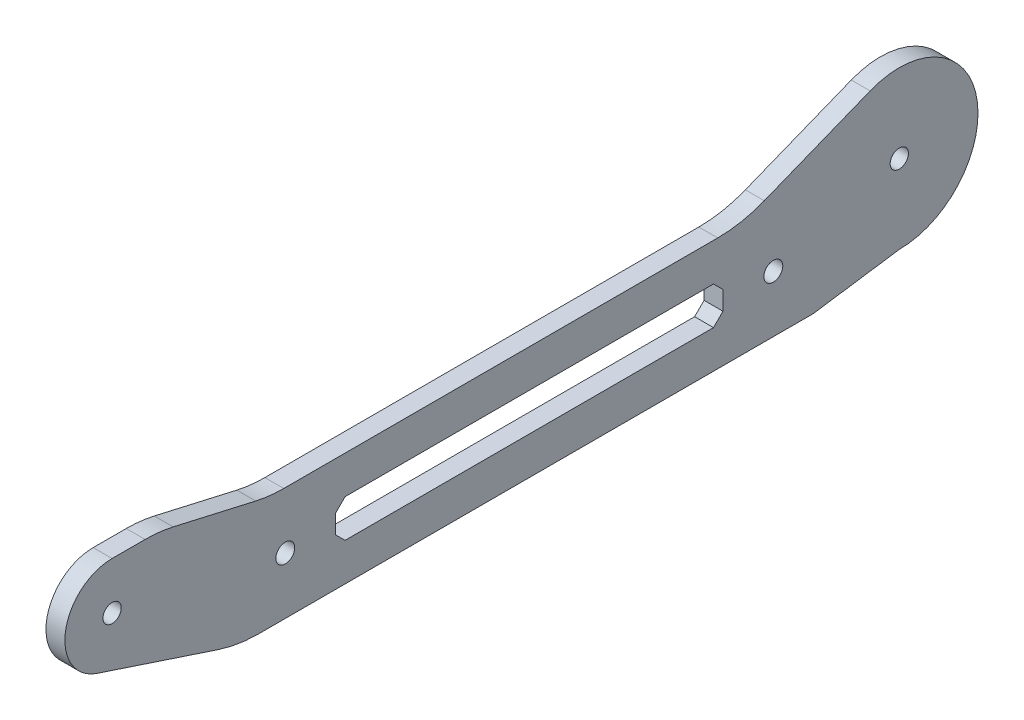
SolidWorks part; units mm, degrees
ref_plane "Front Plane" through (0, 0, 0) normal (0, 0, 1) x (1, 0, 0)
ref_plane "Top Plane" through (0, 0, 0) normal (0, 1, 0) x (1, 0, 0)
ref_plane "Right Plane" through (0, 0, 0) normal (1, 0, 0) x (0, 0, -1)
sketch "Sketch1" plane through (0, 0, 0) normal (1, 0, 0) x (0, 0, -1)
  line L0 (0, 0) -> (-125, 0) construction
  line L1 (-105, -14.5) -> (-13.675, -14.5)
  line L2 (-105, -14.5) -> (-127.351, -7.122)
  line L3 (-125, 7.5) -> (-117.5, 7.5)
  line L4 (-117.5, 7.5) -> (-100, 3.5)
  line L5 (-100, 3.5) -> (-25, 3.5)
  line L6 (-25, 3.5) -> (-4.6241, 11.6132)
  line L7 (-89.5, -4) -> (-88, -2.5)
  line L8 (-60, -5.5) -> (-97.5, -5.5) construction
  line L9 (-60, -5.5) -> (-20, -5.5) construction
  line L10 (-88, -2.5) -> (-29.5, -2.5)
  line L11 (-89.5, -4) -> (-89.5, -7)
  line L12 (-88, -8.5) -> (-29.5, -8.5)
  line L13 (-13.675, -14.5) -> (0, -12.5)
  line L14 (-28, -4) -> (-28, -7)
  line L15 (-89.5, -7) -> (-88, -8.5)
  line L16 (-29.5, -2.5) -> (-28, -4)
  line L17 (-29.5, -8.5) -> (-28, -7)
  line L19 (0, 0) -> (7.675, 0) construction
  line L20 (7.675, 0) -> (10.675, 0) construction
  line L21 (10.675, 0) -> (13.675, 0) construction
  circle A0 centre (3.8375, -6.6467) radius 1.075 construction
  circle A1 centre (5.3375, -9.2448) radius 1.075 construction
  circle A2 centre (6.8375, -11.8429) radius 1.075 construction
  circle A3 centre (-3.8375, -6.6467) radius 1.075 construction
  circle A4 centre (-5.3375, -9.2448) radius 1.075 construction
  circle A5 centre (-6.8375, -11.8429) radius 1.075 construction
  circle A6 centre (-7.675, 0) radius 1.075 construction
  circle A7 centre (-10.675, 0) radius 1.075 construction
  circle A8 centre (-13.675, 0) radius 1.075 construction
  circle A9 centre (-3.8375, 6.6467) radius 1.075 construction
  circle A10 centre (-5.3375, 9.2448) radius 1.075 construction
  circle A11 centre (-6.8375, 11.8429) radius 1.075 construction
  circle A12 centre (3.8375, 6.6467) radius 1.075 construction
  circle A13 centre (5.3375, 9.2448) radius 1.075 construction
  circle A14 centre (6.8375, 11.8429) radius 1.075 construction
  circle A15 centre (-125, 0) radius 1.45
  circle A16 centre (-125, 0) radius 7.5
  circle A17 centre (0, 0) radius 12.5
  circle A18 centre (0, 0) radius 1.45
  circle A19 centre (7.675, 0) radius 1.075 construction
  circle A20 centre (10.675, 0) radius 1.075 construction
  circle A21 centre (13.675, 0) radius 1.075 construction
  circle A22 centre (-97.5, -5.5) radius 1.5
  circle A23 centre (-20, -5.5) radius 1.5
  point P1 (-1.45, 0)
  point P35 (0, 0)
  point P36 (8.75, 0)
  point P37 (6.6, 0)
  point P38 (11.75, 0)
  point P48 (-89.5, -2.5)
  point P56 (-28, -8.5)
  point P63 (-89.5, -8.5)
  point P64 (-28, -2.5)
  dimension "D2" = 6
  dimension "D3" = 125
  dimension "D6" = 2.15
  dimension "D10" = 2.9
  dimension "D5" = 2.9
  dimension "D8" = 25
  dimension "D9" = 15
  dimension "D12" = 25
  dimension "D13" = 25
  dimension "D19" = 6
  dimension "D14" = 7.5
  dimension "D16" = 20
  dimension "D17" = 3
  dimension "D18" = 27.5
  dimension "D20" = 6
  dimension "D21" = 5.5
  dimension "D22" = 13.675
  dimension "D24" = 20
  dimension "D25" = 77.5
  dimension "D26" = 65
  dimension "D4" = 3
  dimension "D7" = 7.675
  dimension "D11" = 3.5
  dimension "D15" = 14.5
  dimension "D23" = 12.5
  dimension "D27" = 8
  dimension "D28" = 8
extrude "Boss-Extrude1" add sketch "Sketch1" along normal mid plane 3
fillet "Fillet1" radius 20 4 edges at (0, 7.5, 117.5) (0, 3.5, 100) (0, 3.5, 25) (0, -14.5, 105)
